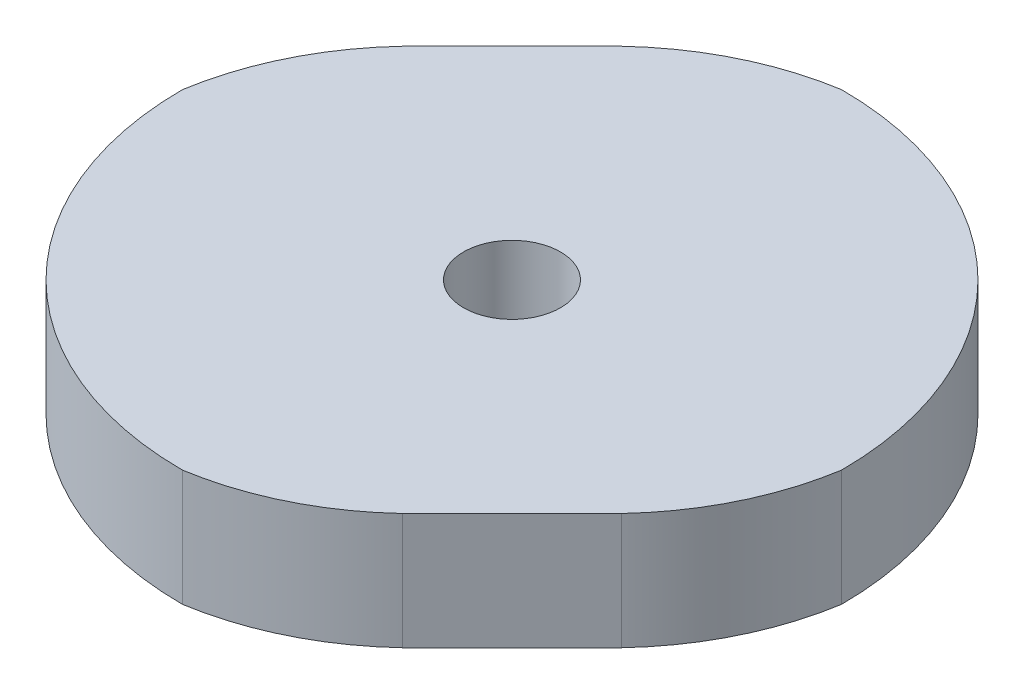
SolidWorks part; units mm, degrees
ref_plane "Front Plane" through (0, 0, 0) normal (0, 0, 1) x (1, 0, 0)
ref_plane "Top Plane" through (0, 0, 0) normal (0, 1, 0) x (1, 0, 0)
ref_plane "Right Plane" through (0, 0, 0) normal (1, 0, 0) x (0, 0, -1)
sketch "Sketch1" plane through (0, 0, 0) normal (0, 1, 0) x (1, 0, 0)
  line L0 (0, 8.5) -> (0, -8.5) construction
  line L1 (-8.5, 0) -> (8.5, 0) construction
  line L2 (6.6323, -3.8055) -> (3.8055, -6.6323)
  line L3 (0, 0) -> (5.2189, -5.2189) construction
  line L5 (-3.8055, 6.6323) -> (-6.6323, 3.8055)
  arc A0 (8.5, 0) -> (0, 8.5) centre (0, 0) ccw
  arc A1 (0, -8.5) -> (4.1355, -6.3022) centre (-1.1494, -1.3473) ccw
  arc A2 (8.5, 0) -> (6.3022, -4.1355) centre (1.3473, 1.1494) cw
  arc A3 (0, 8.5) -> (-4.1355, 6.3022) centre (1.1494, 1.3473) ccw
  arc A4 (-8.5, 0) -> (-6.3022, 4.1355) centre (-1.3473, -1.1494) cw
  arc A5 (-8.5, 0) -> (0, -8.5) centre (0, 0) ccw
  circle A6 centre (0, 0) radius 1.25
  point P11 (5.2189, -5.2189)
  point P16 (0, 0)
  dimension "D1" = 17
  dimension "D2" = 2.5
extrude "Boss-Extrude1" add sketch "Sketch1" along normal blind 3 contours A4 A5 A1 L2 A2 A0 A3 L5 A6
